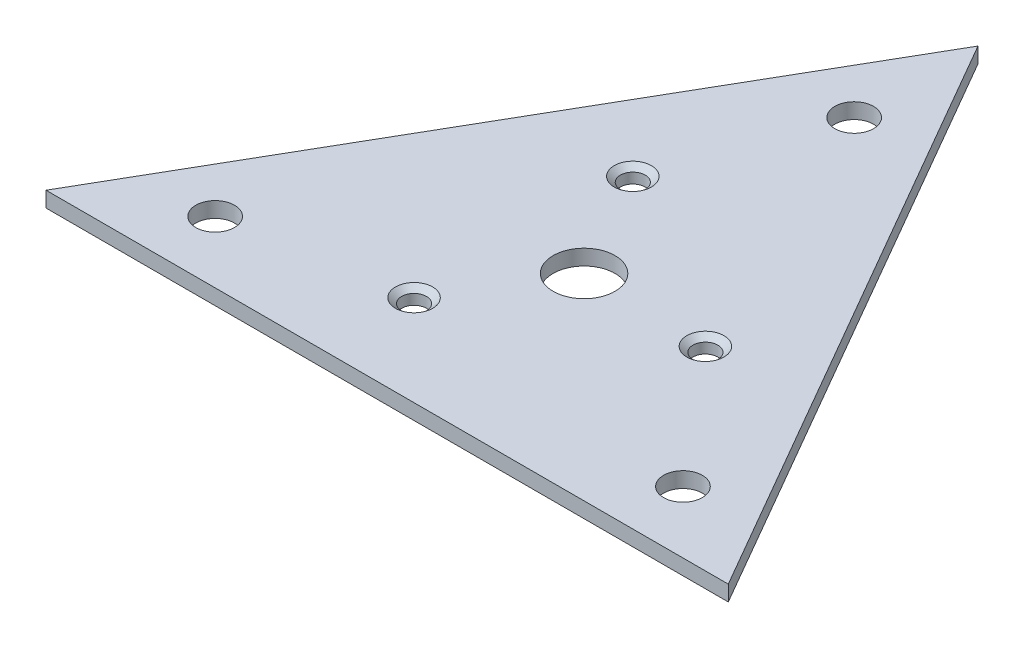
SolidWorks part; units mm, degrees
ref_plane "Front Plane" through (0, 0, 0) normal (0, 0, 1) x (1, 0, 0)
ref_plane "Top Plane" through (0, 0, 0) normal (0, 1, 0) x (1, 0, 0)
ref_plane "Right Plane" through (0, 0, 0) normal (1, 0, 0) x (0, 0, -1)
sketch "Sketch1" plane through (0, 0, 0) normal (0, 1, 0) x (1, 0, 0)
  line L0 (0, 0) -> (139.954, 0)
  line L1 (69.977, 121.2037) -> (139.954, 0)
  line L2 (69.977, 121.2037) -> (0, 0)
  line L3 (69.977, 40.4012) -> (69.977, 121.2037) construction
  line L4 (69.977, 40.4012) -> (0, 0) construction
  line L5 (69.977, 40.4012) -> (139.954, 0) construction
  circle A0 centre (69.977, 40.4012) radius 6.35
  circle A1 centre (117.957, 12.7) radius 3.9687
  circle A2 centre (21.997, 12.7) radius 3.9687
  circle A3 centre (69.977, 95.8037) radius 3.9687
  dimension "D4" = 12.7
  dimension "D5" = 30
  dimension "D7" = 7.9375
  dimension "D8" = 7.9375
  dimension "D10" = 7.9375
  dimension "D1" = 139.954
  dimension "D2" = 139.954
  dimension "D3" = 60
  dimension "D6" = 25.4
  dimension "D9" = 25.4
  dimension "D11" = 25.4
extrude "Boss-Extrude1" add sketch "Sketch1" along normal blind 3.175
sketch "Sketch2" plane through (0, 0, 0) normal (0, 1, 0) x (1, 0, 0)
  line L0 (117.957, 12.7) -> (21.997, 12.7) construction
  line L1 (21.997, 12.7) -> (69.977, 95.8037) construction
  line L2 (69.977, 95.8037) -> (117.957, 12.7) construction
  circle A0 centre (93.967, 54.2519) radius 6.35
  circle A1 centre (69.977, 12.7) radius 6.35
  circle A2 centre (45.987, 54.2519) radius 6.35
  dimension "D1" = 12.7
  dimension "D2" = 12.7
  dimension "D3" = 12.7
extrude "Cut-Extrude1" cut sketch "Sketch2" along normal blind 0.254
hole_wizard "1/4-20 Tapped Hole1" positions "Sketch3" profile "Sketch4" tap size "1/4-20" standard "ANSI Inch" end condition through all
sketch "Sketch3" plane through (0, 3.175, 0) normal (0, 1, 0) x (1, 0, 0)
  point P0 (56.8373, 18.664)
  point P2 (95.3719, 39.8906)
  point P4 (57.7218, 62.6492)
  point P7 (56.8373, 18.664)
  point P8 (95.3719, 39.8906)
  point P9 (57.7218, 62.6492)
sketch "Sketch4" plane through (56.8373, 3.175, -18.664) normal (1, 0, 0) x (0, 0, 1)
  line L0 (0, 0) -> (0, 3.175)
  line L1 (0, 3.175) -> (2.5527, 3.175)
  line L2 (2.5527, 3.175) -> (2.5527, 1.055)
  line L3 (2.5527, 1.055) -> (3.81, 0)
  line L5 (3.81, 0) -> (0, 0)
  line L6 (-2.5527, 1.055) -> (-3.81, 0) construction
  line L11 (0, -6.35) -> (0, 107.95) construction
  dimension "Thru Tap Drill Dia." = 5.1054
  dimension "Thru Tap Drill Depth" = 3.175
  dimension "Near C'Sink Dia." = 7.62
  dimension "Near C'Sink Angle" = 100
cosmetic thread "Hole Thread1" parameters "D2"=6.35
cosmetic thread "Hole Thread2" parameters "D2"=6.35
cosmetic thread "Hole Thread3" parameters "D2"=6.35
